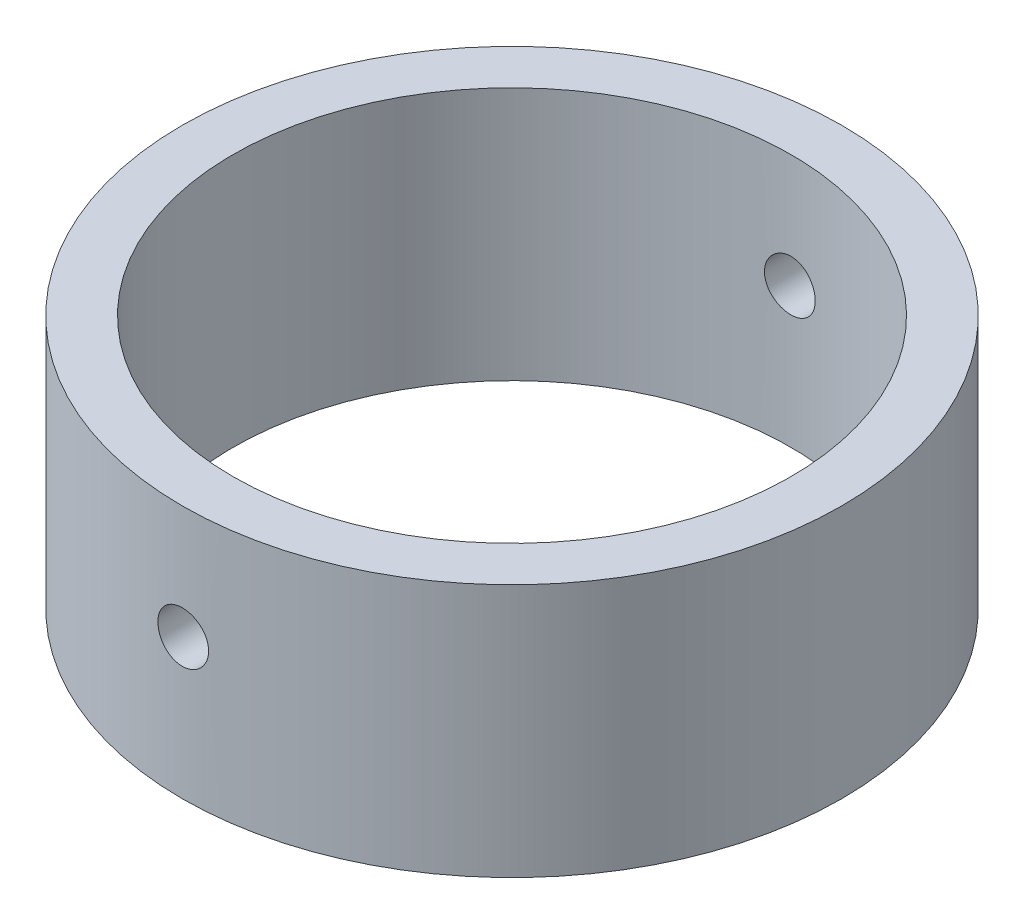
SolidWorks part; units mm, degrees
ref_plane "前视基准面" through (0, 0, 0) normal (0, 0, 1) x (1, 0, 0)
ref_plane "上视基准面" through (0, 0, 0) normal (0, 1, 0) x (1, 0, 0)
ref_plane "右视基准面" through (0, 0, 0) normal (1, 0, 0) x (0, 0, -1)
sketch "草图1" plane through (0, 0, 0) normal (0, 1, 0) x (1, 0, 0)
  circle A0 centre (0, 0) radius 11
  circle A1 centre (0, 0) radius 13
  dimension "D1" = 26
  dimension "D2" = 22
extrude "凸台-拉伸1" add sketch "草图1" along normal blind 10
ref_plane "基准面1" through (0, 0, -13) normal (0, 0, -1) x (-1, 0, 0)
sketch "草图2" plane through (0, 0, -13) normal (0, 0, -1) x (-1, 0, 0)
  circle A0 centre (0, 5.523) radius 1
  point P2 (0, 0)
  dimension "D1" = 2
extrude "切除-拉伸1" cut sketch "草图2" against normal through all
